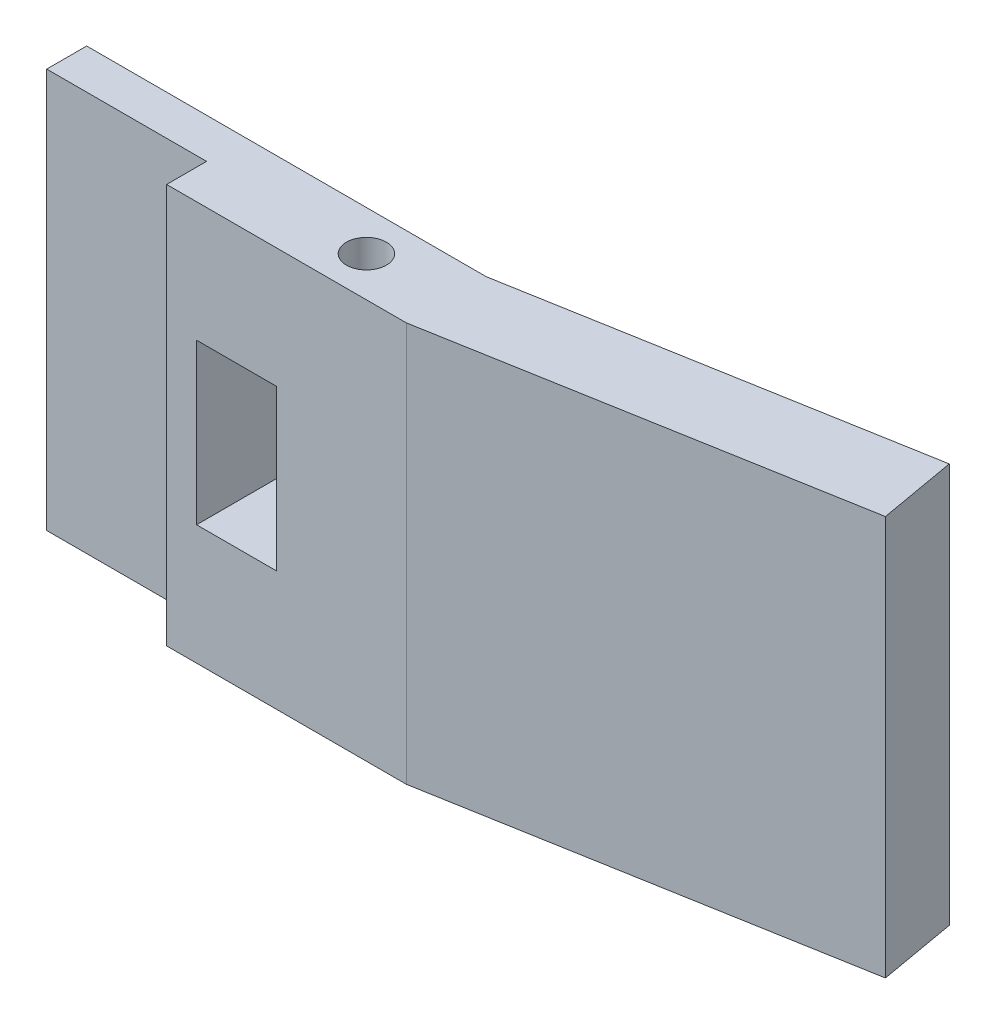
SolidWorks part; units mm, degrees
ref_plane "Front Plane" through (0, 0, 0) normal (0, 0, 1) x (1, 0, 0)
ref_plane "Top Plane" through (0, 0, 0) normal (0, 1, 0) x (1, 0, 0)
ref_plane "Right Plane" through (0, 0, 0) normal (1, 0, 0) x (0, 0, -1)
sketch "Sketch1" plane through (0, 0, 0) normal (0, 1, 0) x (1, 0, 0)
  line L4 (31.75, 0) -> (63.0176, 5.5133)
  line L5 (0, 0) -> (12.7, 0)
  line L6 (0, 0) -> (0, -3.175)
  line L7 (0, -3.175) -> (12.7, -3.175)
  line L8 (12.7, 0) -> (12.7, -3.175)
  line L9 (12.7, 0) -> (31.75, 0)
  line L10 (12.7, 0) -> (12.7, -6.35)
  line L11 (12.7, -6.35) -> (31.75, -6.35)
  line L12 (31.75, 0) -> (31.75, -6.35)
  line L13 (63.0176, 5.5133) -> (64.1036, -0.6452)
  line L14 (64.1036, -0.6452) -> (31.75, -6.35)
  line L15 (31.75, -6.35) -> (64.2, -6.35) construction
  circle A0 centre (25.4, -3.175) radius 1.5875
  dimension "D8" = 3.175
  dimension "D1" = 3.175
  dimension "D2" = 12.7
  dimension "D3" = 6.35
  dimension "D4" = 19.05
  dimension "D5" = 10
  dimension "D6" = 31.75
  dimension "D7" = 25.4
extrude "Boss-Extrude1" add sketch "Sketch1" along normal blind 31.75 contours L14 L13 L4 L12 | L12 L9 L8 L10 L11
sketch "Sketch2" plane through (0, 0, 6.35) normal (0, 0, 1) x (1, 0, 0)
  line L0 (12.7, 31.75) -> (12.7, 0) construction
  line L1 (15.0813, 22.225) -> (21.4312, 22.225)
  line L2 (15.0813, 22.225) -> (15.0813, 9.525)
  line L3 (15.0813, 9.525) -> (21.4312, 9.525)
  line L4 (21.4312, 22.225) -> (21.4312, 9.525)
  line L5 (26.9875, 31.75) -> (23.8125, 31.75) construction
  line L6 (26.9875, 31.75) -> (23.8125, 31.75) construction
  line L7 (23.8125, 31.75) -> (12.7, 31.75) construction
  point P6 (12.7, 15.875)
  point P7 (15.0812, 15.875)
  point P10 (18.2563, 31.75)
  point P13 (18.2563, 22.225)
  dimension "D1" = 6.35
  dimension "D2" = 12.7
extrude "Cut-Extrude1" cut sketch "Sketch2" against normal through all
